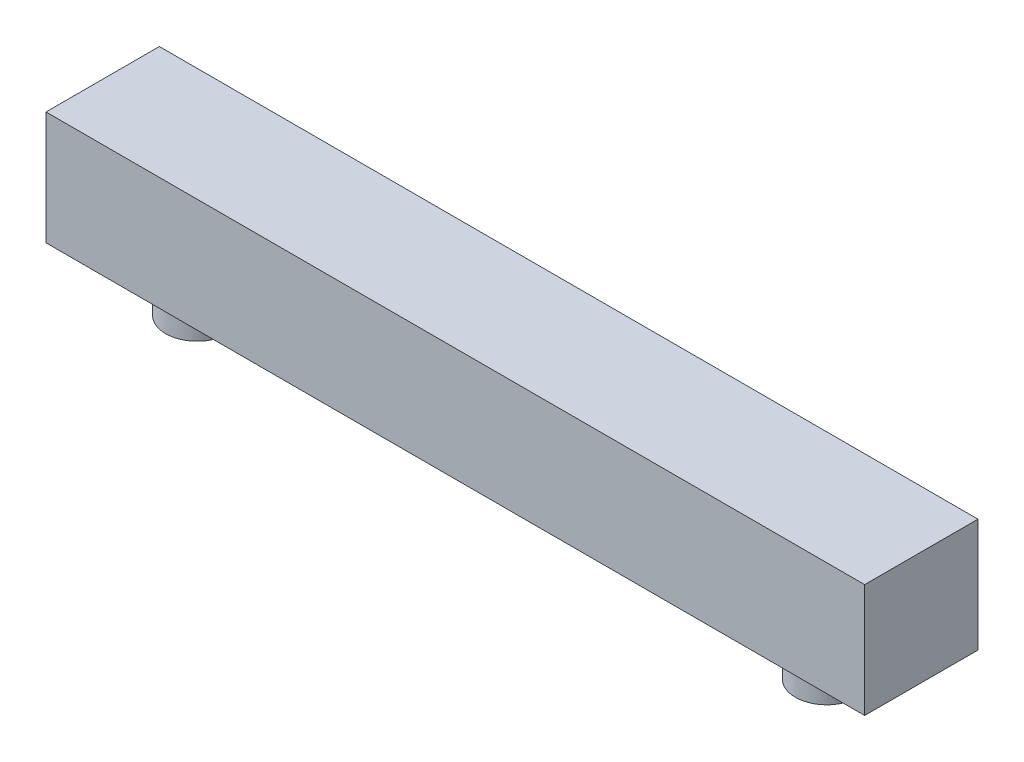
SolidWorks part; units mm, degrees
ref_plane "Front Plane" through (0, 0, 0) normal (0, 0, 1) x (1, 0, 0)
ref_plane "Top Plane" through (0, 0, 0) normal (0, 1, 0) x (1, 0, 0)
ref_plane "Right Plane" through (0, 0, 0) normal (1, 0, 0) x (0, 0, -1)
sketch "Sketch1" plane through (0, 0, 0) normal (0, 1, 0) x (1, 0, 0)
  line L0 (32.5, 0) -> (32.5, -9.7789) construction
  line L1 (0, 0) -> (65, 0)
  line L2 (0, 0) -> (0, -9)
  line L3 (0, -9) -> (65, -9)
  line L4 (65, 0) -> (65, -9)
  dimension "D1" = 65
  dimension "D2" = 9
extrude "Boss-Extrude1" add sketch "Sketch1" along normal blind 9
sketch "Sketch2" plane through (0, 0, 0) normal (0, -1, 0) x (1, 0, 0)
  line L0 (32.5, 9) -> (32.5, 0) construction
  line L2 (0, 9) -> (65, 9) construction
  line L3 (65, 0) -> (0, 0) construction
  circle A0 centre (7.5, 4.5) radius 2.5
  circle A1 centre (57.5, 4.5) radius 2.5
extrude "Boss-Extrude2" add sketch "Sketch2" along normal blind 3.5
